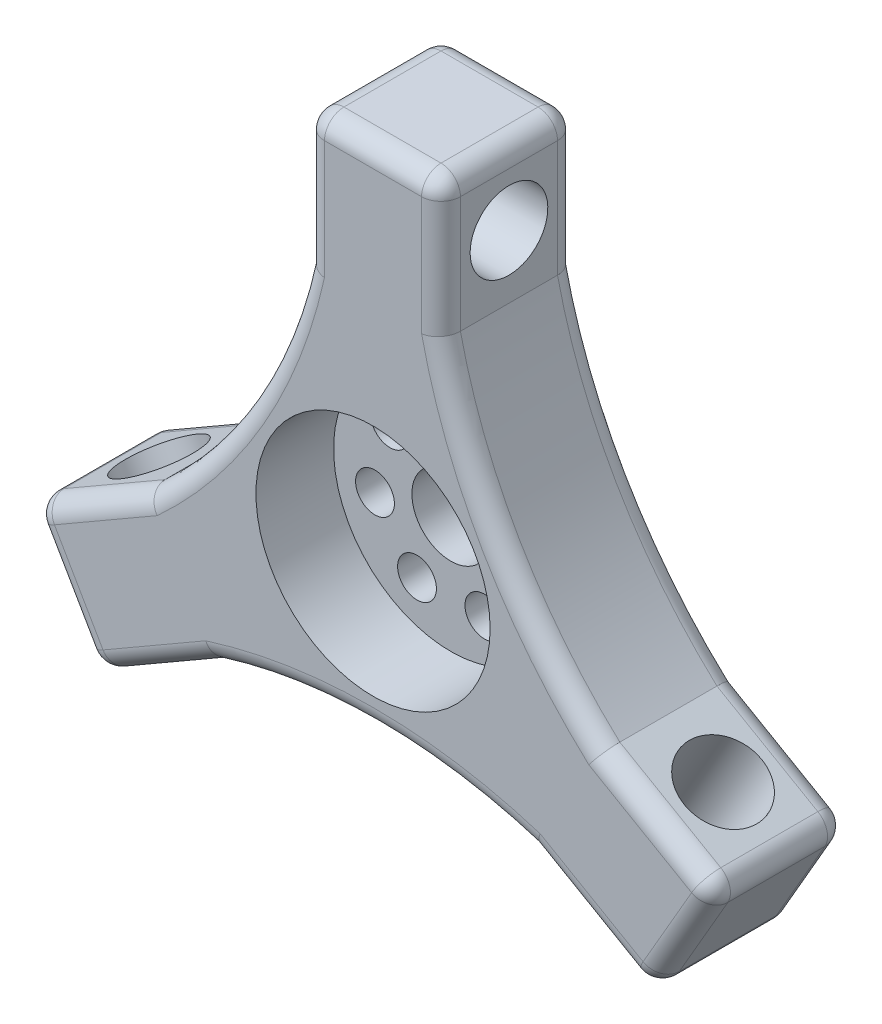
SolidWorks part; units mm, degrees
ref_plane "Front Plane" through (0, 0, 0) normal (0, 0, 1) x (1, 0, 0)
ref_plane "Top Plane" through (0, 0, 0) normal (0, 1, 0) x (1, 0, 0)
ref_plane "Right Plane" through (0, 0, 0) normal (1, 0, 0) x (0, 0, -1)
sketch "Sketch2" plane through (0, 0, 0) normal (0, 0, 1) x (1, 0, 0)
  line L0 (-7, 23) -> (-7, 37)
  line L1 (-7, 37) -> (7, 37)
  line L2 (7, 37) -> (7, 23)
  line L3 (23.4186, -5.4378) -> (35.5429, -12.4378)
  line L4 (35.5429, -12.4378) -> (28.5429, -24.5622)
  line L5 (28.5429, -24.5622) -> (16.4186, -17.5622)
  line L6 (-16.4186, -17.5622) -> (-28.5429, -24.5622)
  line L7 (-28.5429, -24.5622) -> (-35.5429, -12.4378)
  line L8 (-35.5429, -12.4378) -> (-23.4186, -5.4378)
  circle A3 centre (0, 0) radius 4
  arc A4 (7, 23) -> (23.4186, -5.4378) centre (60.6689, 35.0272) ccw
  arc A5 (16.4186, -17.5622) -> (-16.4186, -17.5622) centre (0, -70.0544) ccw
  arc A6 (-23.4186, -5.4378) -> (-7, 23) centre (-60.6689, 35.0272) ccw
  point P9 (0, 37)
  dimension "D1" = 55
  dimension "D3" = 37
  dimension "D5" = 8
  dimension "D2" = 14
  dimension "D6" = 14
  dimension "D7" = 14
  dimension "D9" = 37
  dimension "D10" = 37
  dimension "D11" = 37
  dimension "D4" = 3
  dimension "D8" = 3
extrude "Boss-Extrude1" add sketch "Sketch2" along normal blind 14
sketch "Sketch7" plane through (0, 0, 14) normal (0, 0, 1) x (1, 0, 0)
  circle A0 centre (0, 0) radius 12.0607
extrude "Cut-Extrude4" cut sketch "Sketch7" against normal blind 8
sketch "Sketch8" plane through (0, 0, 6) normal (0, 0, 1) x (1, 0, 0)
  circle A0 centre (0, 8) radius 2
  circle A1 centre (6.2547, 4.9879) radius 2
  circle A2 centre (7.7994, -1.7802) radius 2
  circle A3 centre (3.4711, -7.2078) radius 2
  circle A4 centre (-3.4711, -7.2078) radius 2
  circle A5 centre (-7.7994, -1.7802) radius 2
  circle A6 centre (-6.2547, 4.9879) radius 2
  dimension "D1" = 8
  dimension "D2" = 7
extrude "Cut-Extrude5" cut sketch "Sketch8" against normal blind 8
fillet "Fillet2" radius 2 6 edges at (0, 37, 0) (0, 37, 14) (-32.0429, -18.5, 0) (-32.0429, -18.5, 14) (32.0429, -18.5, 0) (32.0429, -18.5, 14)
sketch "Sketch10" plane through (3.5, 6.0622, 0) normal (0.5, 0.866, 0) x (0.866, -0.5, 0)
  line L0 (37, -12) -> (37, -2) construction
  line L1 (35, -14) -> (23, -14) construction
  circle A0 centre (29.5, -7) radius 4
  dimension "D1" = 8
  dimension "D2" = 7.5
  dimension "D3" = 7
extrude "Cut-Extrude6" cut sketch "Sketch10" against normal up to next
fillet "Fillet4" radius 2 36 edges at (-35.0356, -12.1449, 0.5858) (-35.5429, -12.4378, 7) (-35.0356, -12.1449, 13.4142) (-7, 36.4142, 0.5858) (-7, 37, 7) (-7, 36.4142, 13.4142) (-28.0356, -24.2693, 13.4142) (-28.5429, -24.5622, 7) (-28.0356, -24.2693, 0.5858) (28.0356, -24.2693, 0.5858) (28.5429, -24.5622, 7) (28.0356, -24.2693, 13.4142) (7, 36.4142, 0.5858) (7, 37, 7) (7, 36.4142, 13.4142) (35.0356, -12.1449, 0.5858) (35.5429, -12.4378, 7) (35.0356, -12.1449, 13.4142) (28.6147, -8.4378, 0) (-7, 29, 0) (-13.0375, 7.5272, 0) (-28.6147, -8.4378, 0) (-28.6147, -8.4378, 14) (-13.0375, 7.5272, 14) (-7, 29, 14) (-21.6147, -20.5622, 14) (-21.6147, -20.5622, 0) (21.6147, -20.5622, 0) (21.6147, -20.5622, 14) (7, 29, 0) (13.0375, 7.5272, 0) (0, -15.0544, 0) (0, -15.0544, 14) (7, 29, 14) (28.6147, -8.4378, 14) (13.0375, 7.5272, 14)
pattern_circular "CirPattern1" count 3 over 360 about axis through (0, 0, 6) along (0, 0, 1) of "Cut-Extrude6"
